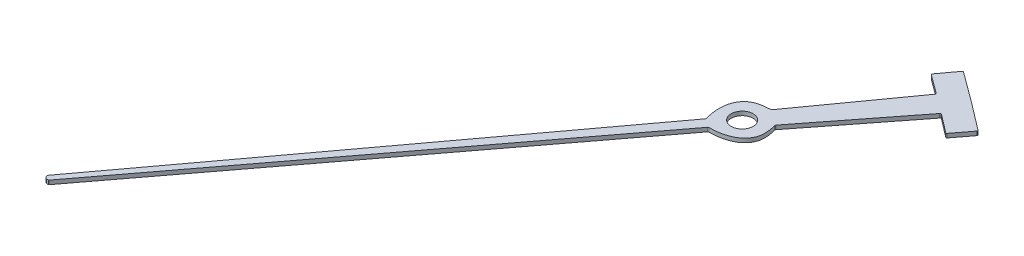
SolidWorks part; units mm, degrees
ref_plane "Front Plane" through (0, 0, 0) normal (0, 0, 1) x (1, 0, 0)
ref_plane "Top Plane" through (0, 0, 0) normal (0, 1, 0) x (1, 0, 0)
ref_plane "Right Plane" through (0, 0, 0) normal (1, 0, 0) x (0, 0, -1)
sketch "Sketch1" plane through (0, 0, 0) normal (0, 1, 0) x (1, 0, 0)
  line L0 (92.0851, 127.1039) -> (-106.0885, -137.707) construction
  line L1 (92.0851, 127.1039) -> (77.1781, 138.0623)
  line L2 (77.1781, 138.0623) -> (70.3603, 128.7877)
  line L3 (70.3603, 128.7877) -> (80.3709, 121.4288)
  line L4 (80.3709, 121.4288) -> (45.8767, 73.3074)
  line L5 (33.451, 53.1263) -> (-106.7999, -136.1812)
  line L6 (37.6462, 49.9869) -> (-104.424, -137.9592)
  line L7 (89.9439, 114.2647) -> (53.5038, 67.5996)
  line L8 (99.8273, 106.7358) -> (89.9439, 114.2647)
  line L9 (106.8027, 115.8925) -> (99.8273, 106.7358)
  line L10 (92.0851, 127.1039) -> (106.8027, 115.8925)
  arc A0 (-104.424, -137.9592) -> (-106.7999, -136.1812) centre (-105.021, -136.2806) cw
  spline S0 degree 3 poles (33.451, 53.1263) (31.2159, 60.4949) (32.4471, 70.4466) (40.8621, 73.1676) (45.8767, 73.3074) knots 0 0 0 0 0.641849 1 1 1 1
  spline S1 degree 3 poles (37.6462, 49.9869) (45.346, 49.9205) (54.5466, 53.9084) (54.7839, 62.7491) (53.5038, 67.5996) knots 0 0 0 0 0.641849 1 1 1 1
extrude "Boss-Extrude1" add sketch "Sketch1" along normal blind 2
fillet "Fillet2" radius 0.5 12 edges at (-104.424, 1, 137.9592) (-106.7999, 1, 136.1812) (33.451, 1, -53.1263) (37.6462, 1, -49.9869) (45.8767, 1, -73.3074) (53.5038, 1, -67.5996) (99.8273, 1, -106.7358) (89.9439, 1, -114.2647) (80.3709, 1, -121.4288) (70.3603, 1, -128.7877) (77.1781, 1, -138.0623) (106.8027, 1, -115.8925)
sketch "Sketch2" plane through (0, 2, 0) normal (0, 1, 0) x (1, 0, 0)
  line L0 (92.0851, 127.1039) -> (-106.0885, -137.707) construction
  arc A0 (-106.8002, -136.3738) -> (-104.6086, -138.0139) centre (-105.021, -136.2806) ccw construction
  circle A1 centre (43.0253, 61.5473) radius 5.5
  dimension "D1" = 11
extrude "Cut-Extrude1" cut sketch "Sketch2" against normal through all
scale "Scale1" scale about centroid uniform scaling yes scale factor 0.05848
